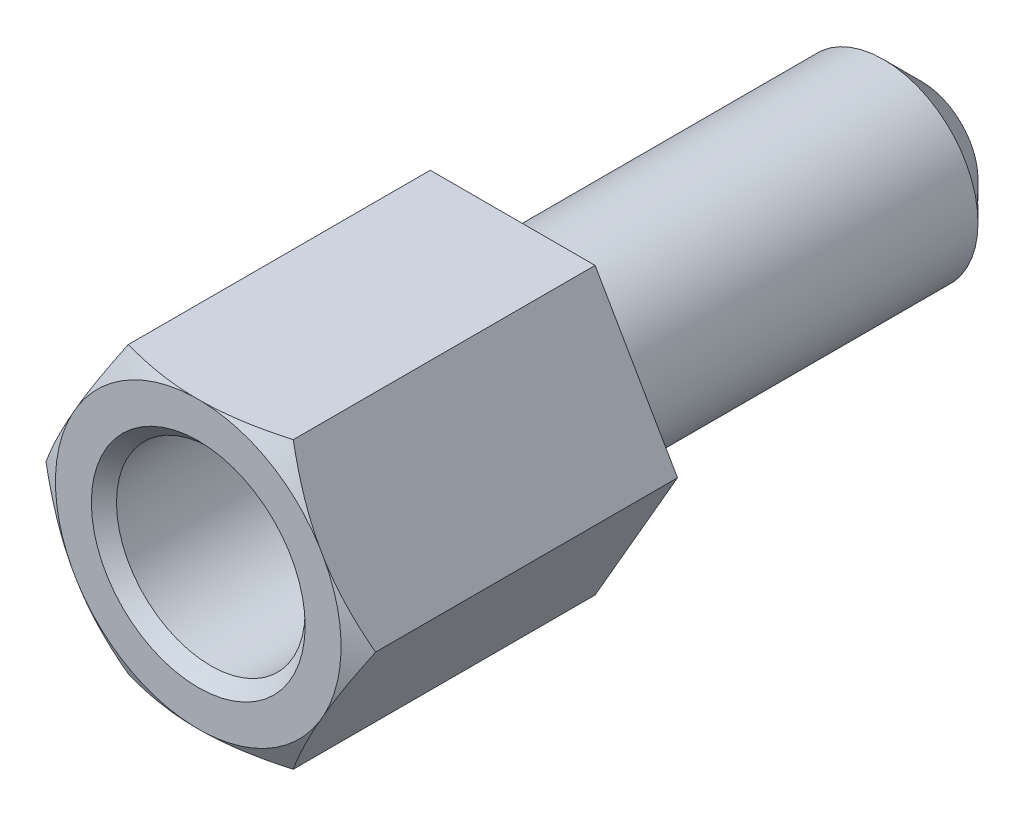
SolidWorks part; units mm, degrees
ref_plane "Front Plane" through (0, 0, 0) normal (0, 0, 1) x (1, 0, 0)
ref_plane "Top Plane" through (0, 0, 0) normal (0, 1, 0) x (1, 0, 0)
ref_plane "Right Plane" through (0, 0, 0) normal (1, 0, 0) x (0, 0, -1)
sketch "Sketch1" plane through (0, 0, 0) normal (0, 0, 1) x (1, 0, 0)
  line L0 (0, 0) -> (2.6212, 0) construction
  line L1 (2.6212, 0) -> (1.3106, 2.27)
  line L2 (1.3106, 2.27) -> (-1.3106, 2.27)
  line L3 (-1.3106, 2.27) -> (-2.6212, 0)
  line L4 (-2.6212, 0) -> (-1.3106, -2.27)
  line L5 (-1.3106, -2.27) -> (1.3106, -2.27)
  line L6 (1.3106, -2.27) -> (2.6212, 0)
  circle A0 centre (0, 0) radius 2.27 construction
  dimension "D1" = 4.54
extrude "Boss-Extrude1" add sketch "Sketch1" along normal blind 5
sketch "Sketch2" plane through (0, 0, 5) normal (0, 0, 1) x (1, 0, 0)
  circle A0 centre (0, 0) radius 1.5
extrude "Cut-Extrude1" cut sketch "Sketch2" against normal blind 4 and the other way through all
sketch "Sketch3" plane through (0, 0, 0) normal (0, 1, 0) x (1, 0, 0)
  line L0 (-2.6212, -5) -> (-2.2712, -5)
  line L1 (-2.2712, -5) -> (-2.6212, -4.8)
  line L2 (-2.6212, -5) -> (-2.6212, 0) construction
  line L3 (-2.6212, -4.8) -> (-2.6212, -5)
  dimension "D1" = 0.35
  dimension "D2" = 0.2
ref_axis "Axis1" through (0, 0, 1) along (0, 0, 1)
revolve "Cut-Revolve1" cut sketch "Sketch3" angle 360 about axis through (0, 0, 1) along (0, 0, 1)
ref_plane "Plane1" through (0, 0, 2.5) normal (0, 0, 1) x (1, 0, 0)
chamfer "Chamfer1" distance 0.2 angle 45 1 edges at (1.5, 0, 5)
sketch "Sketch4" plane through (0, 0, 0) normal (0, 0, -1) x (-1, 0, 0)
  circle A0 centre (0, 0) radius 1.5
extrude "Boss-Extrude2" add sketch "Sketch4" along normal blind 6.5
chamfer "Chamfer2" distance 0.6 angle 45 1 edges at (-1.5, 0, -6.5)
